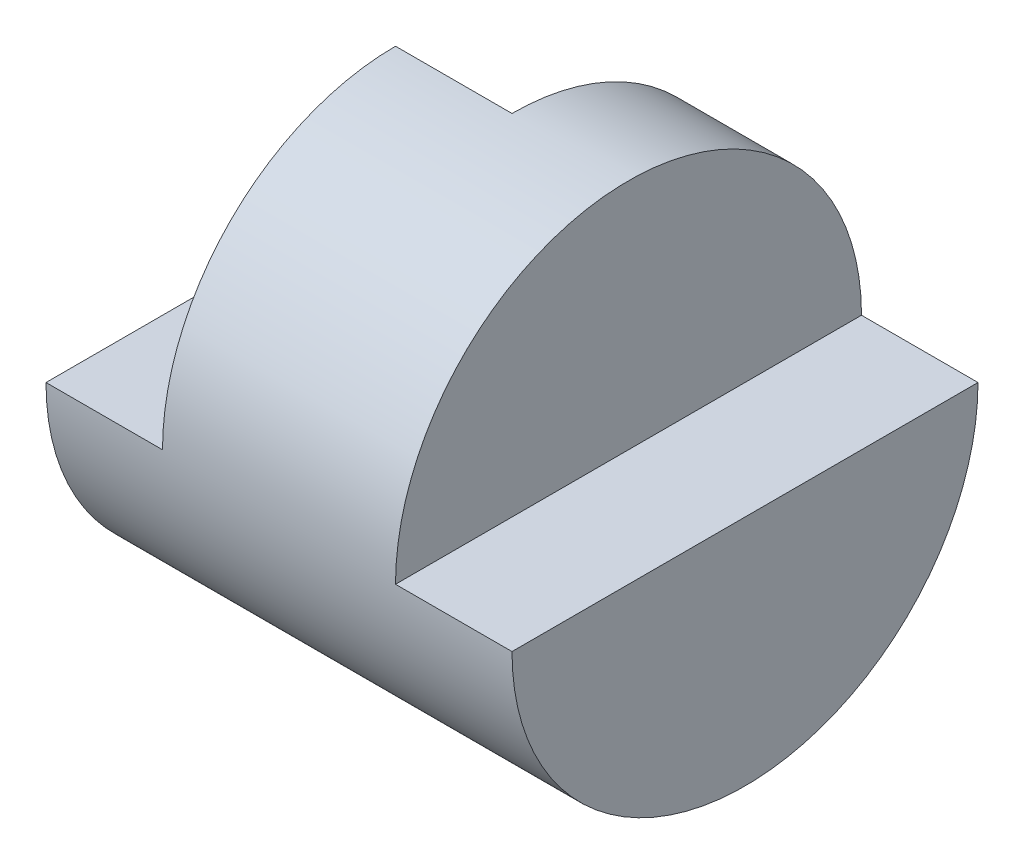
SolidWorks part; units mm, degrees
ref_plane "Front Plane" through (0, 0, 0) normal (0, 0, 1) x (1, 0, 0)
ref_plane "Top Plane" through (0, 0, 0) normal (0, 1, 0) x (1, 0, 0)
ref_plane "Right Plane" through (0, 0, 0) normal (1, 0, 0) x (0, 0, -1)
sketch "Sketch5" plane through (0, 0, 0) normal (0, 0, 1) x (1, 0, 0)
  line L0 (0, 0) -> (4, 0)
  dimension "D1" = 4
revolve "Revolve-Thin2" add sketch "Sketch5" angle 360 about L0 wall 2
sketch "Sketch6" plane through (0, 0, 0) normal (0, 0, 1) x (1, 0, 0)
  line L1 (0, 2) -> (1, 2)
  line L2 (0, 2) -> (0, 0)
  line L3 (0, 0) -> (1, 0)
  line L4 (1, 2) -> (1, 0)
  line L5 (4, 2) -> (3, 2)
  line L6 (4, 2) -> (4, 0)
  line L7 (4, 0) -> (3, 0)
  line L8 (3, 2) -> (3, 0)
  dimension "D1" = 1
  dimension "D2" = 1
  dimension "D3" = 2
  dimension "D4" = 2
extrude "Cut-Extrude5" cut sketch "Sketch6" against normal mid plane 11 contours L5 L8 L7 L6 | L4 L1 L2 L3
sketch "Sketch7" plane through (0, 0, 0) normal (0, 1, 0) x (1, 0, 0)
  line L1 (1, 2) -> (2, 2)
  line L2 (1, 2) -> (1, 0)
  line L3 (1, 0) -> (2, 0)
  line L4 (2, 2) -> (2, 0)
  dimension "D1" = 1
  dimension "D2" = 2
extrude "Cut-Extrude6" cut sketch "Sketch7" along normal blind 3
